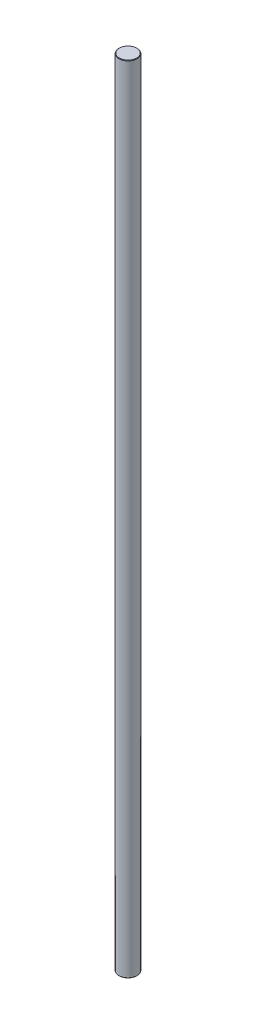
SolidWorks part; units mm, degrees
ref_plane "Front Plane" through (0, 0, 0) normal (0, 0, 1) x (1, 0, 0)
ref_plane "Top Plane" through (0, 0, 0) normal (0, 1, 0) x (1, 0, 0)
ref_plane "Right Plane" through (0, 0, 0) normal (1, 0, 0) x (0, 0, -1)
sketch "Sketch1" plane through (0, 0, 0) normal (0, 1, 0) x (1, 0, 0)
  circle A0 centre (0, 0) radius 4
  dimension "D1" = 8
extrude "Boss-Extrude1" add sketch "Sketch1" along normal mid plane 350
chamfer "Chamfer1" distance 0.2 angle 45 2 edges at (0, -175, 4) (0, 175, 4)
